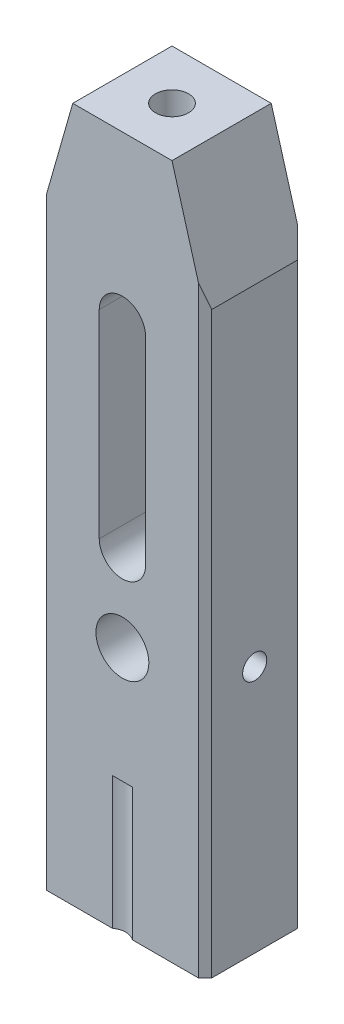
SolidWorks part; units mm, degrees
ref_plane "Front Plane" through (0, 0, 0) normal (0, 0, 1) x (1, 0, 0)
ref_plane "Top Plane" through (0, 0, 0) normal (0, 1, 0) x (1, 0, 0)
ref_plane "Right Plane" through (0, 0, 0) normal (1, 0, 0) x (0, 0, -1)
sketch "Sketch2" plane through (0, 0, 0) normal (0, 1, 0) x (1, 0, 0)
  line L1 (0, 0) -> (50, 0)
  line L2 (0, 0) -> (0, 30)
  line L3 (0, 30) -> (50, 30)
  line L4 (50, 0) -> (50, 30)
  dimension "D1" = 50
  dimension "D2" = 30
extrude "Boss-Extrude2" add sketch "Sketch2" along normal blind 210
sketch "Sketch3" plane through (0, 0, 0) normal (0, 0, 1) x (1, 0, 0)
  line L0 (0, 0) -> (50, 0) construction
  circle A0 centre (25, 75) radius 8
  point P0 (25, 0)
  dimension "D2" = 16
  dimension "D3" = 75
extrude "Cut-Extrude2" cut sketch "Sketch3" against normal up to next contours A0
sketch "Sketch7" plane through (0, 0, 0) normal (0, 0, 1) x (1, 0, 0)
  line L0 (0, 175) -> (10, 210)
  line L1 (25, 210) -> (25, 0) construction
  line L2 (0, 210) -> (50, 210) construction
  line L3 (0, 0) -> (50, 0) construction
  line L4 (0, 0) -> (50, 0)
  line L5 (50, 0) -> (50, 210)
  line L6 (50, 210) -> (0, 210)
  line L7 (0, 210) -> (0, 0)
  line L10 (10, 210) -> (0, 210)
  line L11 (0, 210) -> (0, 175)
  line L12 (0, 175) -> (50, 175) construction
  line L15 (50, 210) -> (50, 175)
  line L16 (40, 210) -> (50, 210)
  line L17 (50, 175) -> (40, 210)
  dimension "D2" = 10
  dimension "D3" = 175
  dimension "D1" = 0
extrude "Cut-Extrude5" cut sketch "Sketch7" against normal up to next contours L10 L11 L0 | L15 L17 L16
sketch "Sketch11" plane through (0, 0, -30) normal (0, 0, -1) x (-1, 0, 0)
  line L0 (-25, 160) -> (-25, 100) construction
  line L1 (-18, 160) -> (-18, 100)
  line L2 (-32, 160) -> (-32, 100)
  line L4 (-50, 0) -> (0, 0) construction
  arc A0 (-18, 160) -> (-32, 160) centre (-25, 160) ccw
  arc A1 (-32, 100) -> (-18, 100) centre (-25, 100) ccw
  point P0 (-25, -54.4382)
  point P3 (-25, 130)
  point P10 (-25, 0)
  dimension "D1" = 100
  dimension "D2" = 60
  dimension "D3" = 14
extrude "Cut-Extrude8" cut sketch "Sketch11" against normal up to next
chamfer "Chamfer3" distance 2 angle 45 4 edges at (0, 87.5, -30) (50, 87.5, -30) (50, 87.5, 0) (0, 87.5, 0)
sketch "Sketch15" plane through (0, 0, 0) normal (0, -1, 0) x (1, 0, 0)
  line L0 (25, 0) -> (25, -30) construction
  line L1 (2, 0) -> (48, 0) construction
  line L2 (48, -30) -> (2, -30) construction
  line L3 (22, 0) -> (28, 0)
  line L4 (0, -15) -> (50, -15) construction
  line L5 (0, -28) -> (0, -2) construction
  line L6 (50, -2) -> (50, -28) construction
  line L7 (22, -30) -> (28, -30)
  arc A0 (22, 0) -> (28, 0) centre (25, 4) ccw
  arc A1 (22, -30) -> (28, -30) centre (25, -34) cw
  dimension "D2" = 5
  dimension "D1" = 6
extrude "Cut-Extrude10" cut sketch "Sketch15" against normal blind 40 contours L3 A0 | A1 L7
sketch "Sketch16" plane through (50, 0, 0) normal (1, 0, 0) x (0, 0, -1)
  line L0 (2, 0) -> (28, 0) construction
  circle A0 centre (15, 75) radius 3.65
  point P5 (15, 0)
  dimension "D2" = 7.3
  dimension "D1" = 75
extrude "Cut-Extrude11" cut sketch "Sketch16" against normal up to surface (50 mm away) up to face at (0, 87.5, -15)
sketch "Sketch20" plane through (0, 210, 0) normal (0, 1, 0) x (1, 0, 0)
  line L0 (10, 30) -> (10, 0) construction
  line L2 (40, 30) -> (10, 30) construction
  circle A0 centre (25, 15) radius 5
  point P2 (10, 15)
  point P6 (25, 30)
  dimension "D1" = 10
extrude "Cut-Extrude13" cut sketch "Sketch20" against normal blind 35
